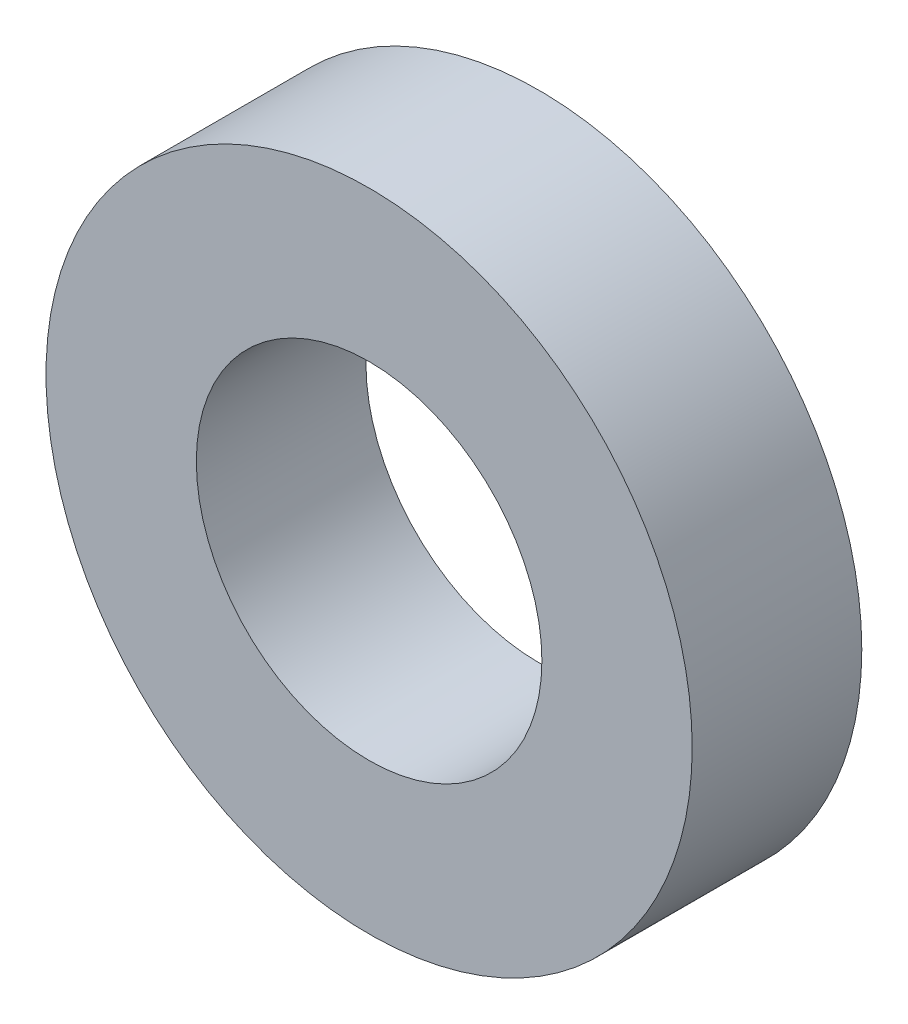
SolidWorks part; units mm, degrees
ref_plane "Front Plane" through (0, 0, 0) normal (0, 0, 1) x (1, 0, 0)
ref_plane "Top Plane" through (0, 0, 0) normal (0, 1, 0) x (1, 0, 0)
ref_plane "Right Plane" through (0, 0, 0) normal (1, 0, 0) x (0, 0, -1)
sketch "Sketch1" plane through (0, 0, 0) normal (0, 0, 1) x (1, 0, 0)
  circle A0 centre (0, 0) radius 20.375
  circle A1 centre (0, 0) radius 38.1
  dimension "D1" = 76.2
  dimension "D2" = 40.75
extrude "Boss-Extrude1" add sketch "Sketch1" along normal blind 20
sketch "Sketch2" plane through (0, 0, 0) normal (0, 0, -1) x (-1, 0, 0)
  line L0 (-27.5, 0) -> (0, 0) construction
  circle A0 centre (-27.5, 0) radius 3.95
  circle A1 centre (-27.5, 0) radius 6.625 construction
  circle A2 centre (-17.146, 21.5004) radius 6.625 construction
  circle A3 centre (-17.146, 21.5004) radius 3.95
  circle A4 centre (6.1193, 26.8105) radius 6.625 construction
  circle A5 centre (6.1193, 26.8105) radius 3.95
  circle A6 centre (24.7766, 11.9318) radius 6.625 construction
  circle A7 centre (24.7766, 11.9318) radius 3.95
  circle A8 centre (24.7766, -11.9318) radius 6.625 construction
  circle A9 centre (24.7766, -11.9318) radius 3.95
  circle A10 centre (6.1193, -26.8105) radius 6.625 construction
  circle A11 centre (6.1193, -26.8105) radius 3.95
  circle A12 centre (-17.146, -21.5004) radius 6.625 construction
  circle A13 centre (-17.146, -21.5004) radius 3.95
  point P6 (0, 0)
  point P25 (0, 0)
  dimension "D1" = 7.9
  dimension "D2" = 13.25
  dimension "D3" = 27.5
  dimension "D4" = 7
extrude "Cut-Extrude1" [suppressed] cut sketch "Sketch2" against normal through all
sketch "Sketch4" [suppressed] plane through (0, 0, 0) normal (0, 0, -1) x (-1, 0, 0)
  circle A1 centre (-17.146, 21.5004) radius 6.75
  circle A2 centre (6.1193, 26.8105) radius 6.75
  circle A3 centre (24.7766, 11.9318) radius 6.75
  circle A4 centre (24.7766, -11.9318) radius 6.75
  circle A5 centre (6.1193, -26.8105) radius 6.75
  circle A6 centre (-17.146, -21.5004) radius 6.75
  circle A7 centre (-27.5, 0) radius 6.75
  point P1 (0, 0)
  point P17 (0, 0)
  dimension "D1" = 13.5
  dimension "D2" = 7
extrude "Cut-Extrude2" [suppressed] cut sketch "Sketch4" against normal blind 6.5
